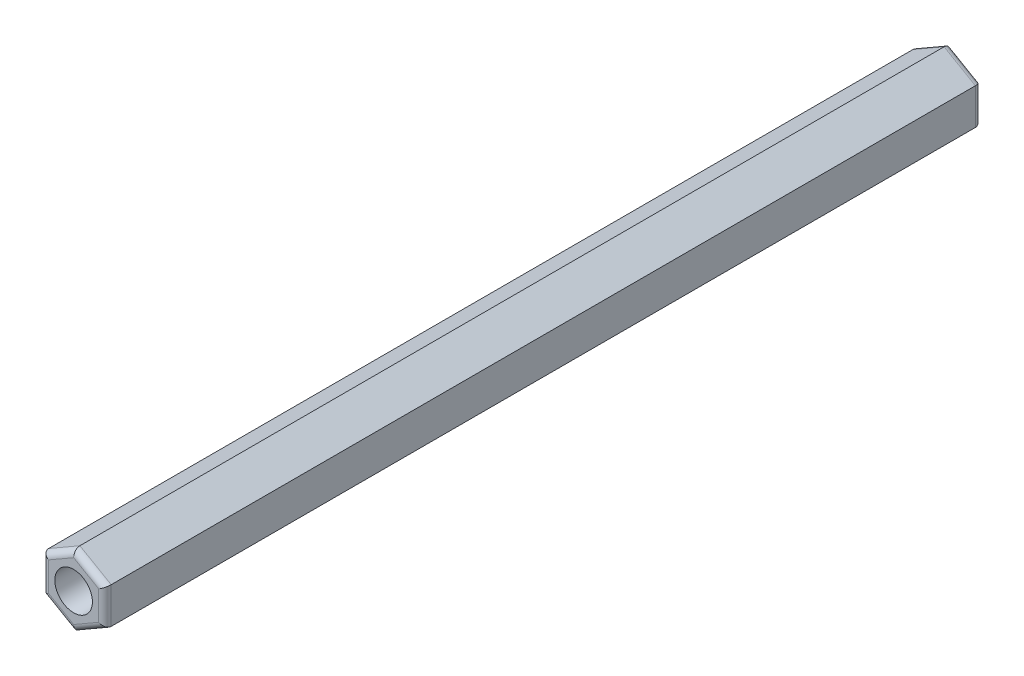
SolidWorks part; units mm, degrees
material "Liga de aço fundido"
ref_plane "Plano frontal" through (0, 0, 0) normal (0, 0, 1) x (1, 0, 0)
ref_plane "Plano superior" through (0, 0, 0) normal (0, 1, 0) x (1, 0, 0)
ref_plane "Plano direito" through (0, 0, 0) normal (1, 0, 0) x (0, 0, -1)
ref_plane "Plano1" through (0, 0, 0) normal (0, 0, -1) x (-1, 0, 0)
sketch "Esboço1" plane through (0, 0, 0) normal (0, 0, -1) x (-1, 0, 0)
  line L0 (67.5021, -1.4434) -> (70.0021, -2.8868)
  line L1 (70.0021, -2.8868) -> (72.5021, -1.4434)
  line L2 (72.5021, -1.4434) -> (72.5021, 1.4434)
  line L3 (72.5021, 1.4434) -> (70.0021, 2.8868)
  line L4 (70.0021, 2.8868) -> (67.5021, 1.4434)
  line L5 (67.5021, 1.4434) -> (67.5021, -1.4434)
extrude "Ressalto-extrusão1" add sketch "Esboço1" against normal blind 70
fillet "Filete1" radius 0.5 12 edges at (-71.2521, 2.1651, 0) (-72.5021, 0, 0) (-68.7521, 2.1651, 0) (-71.2521, -2.1651, 0) (-67.5021, 0, 0) (-68.7521, -2.1651, 0) (-71.2521, 2.1651, 70) (-72.5021, 0, 70) (-68.7521, 2.1651, 70) (-71.2521, -2.1651, 70) (-67.5021, 0, 70) (-68.7521, -2.1651, 70)
sketch "Esboço2" plane through (0, 0, 70) normal (0, 0, 1) x (1, 0, 0)
  circle A0 centre (-70.0021, 0) radius 1.5
  dimension "D1" = 3
extrude "Corte-extrusão1" cut sketch "Esboço2" against normal through all
